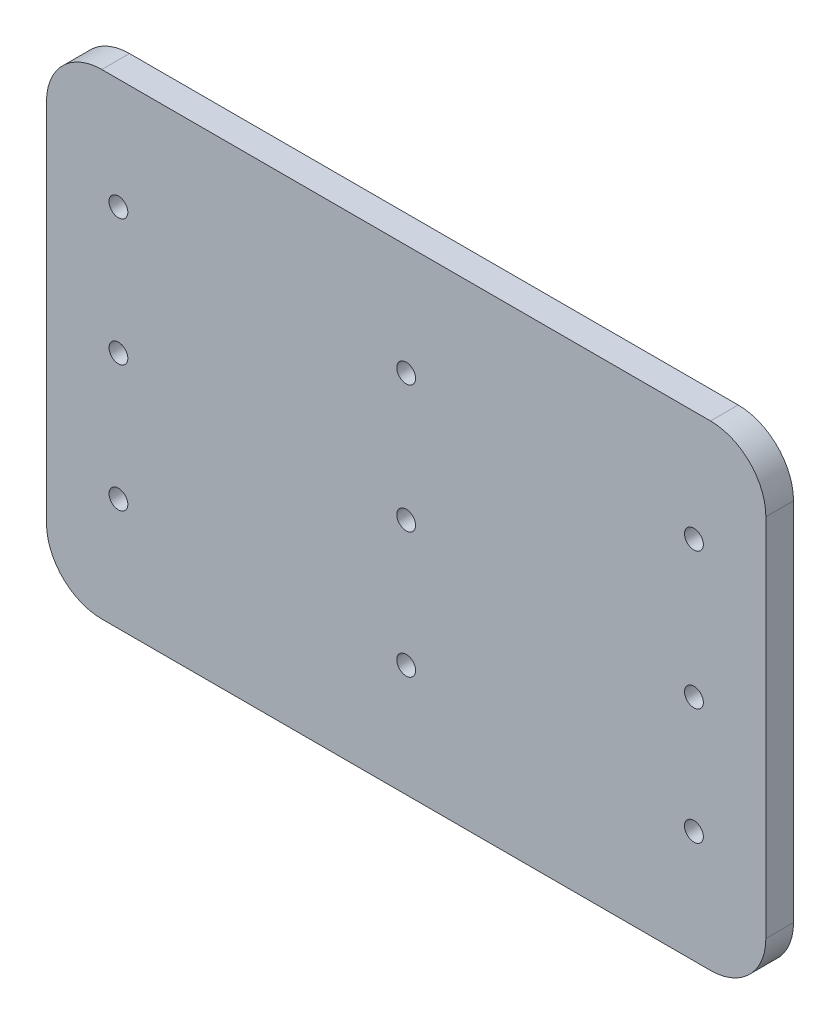
SolidWorks part; units mm, degrees
ref_plane "Front Plane" through (0, 0, 0) normal (0, 0, 1) x (1, 0, 0)
ref_plane "Top Plane" through (0, 0, 0) normal (0, 1, 0) x (1, 0, 0)
ref_plane "Right Plane" through (0, 0, 0) normal (1, 0, 0) x (0, 0, -1)
sketch "Sketch1" plane through (0, 0, 0) normal (0, 0, 1) x (1, 0, 0)
  line L0 (-52, 23) -> (52, 23) construction
  line L1 (-55, 43) -> (55, 43)
  line L2 (-65, 33) -> (-65, -33)
  line L3 (-55, -43) -> (55, -43)
  line L4 (65, 33) -> (65, -33)
  line L5 (-65, 43) -> (65, -43) construction
  line L6 (-65, -43) -> (65, 43) construction
  line L7 (-65, 43) -> (-52, 43)
  line L8 (-65, 43) -> (-65, 23)
  line L9 (-65, 23) -> (-52, 23)
  line L10 (-52, 43) -> (-52, 23)
  line L11 (-52, 23) -> (-52, -22.72) construction
  arc A0 (-65, 33) -> (-55, 43) centre (-55, 33) cw
  arc A1 (-55, -43) -> (-65, -33) centre (-55, -33) cw
  arc A2 (55, -43) -> (65, -33) centre (55, -33) ccw
  arc A3 (65, 33) -> (55, 43) centre (55, 33) ccw
  circle A4 centre (-52, 23) radius 1.7
  circle A5 centre (-52, -22.72) radius 1.7
  circle A6 centre (52, 23) radius 1.7
  circle A7 centre (52, -22.72) radius 1.7
  circle A8 centre (-52, 0.14) radius 1.7
  circle A9 centre (0, 0) radius 1.7
  circle A10 centre (0, -22.72) radius 1.7
  circle A11 centre (0, 23) radius 1.7
  circle A12 centre (52, -1.7) radius 1.7
  point P0 (0, 0)
  dimension "D3" = 10
  dimension "D4" = 10
  dimension "D5" = 10
  dimension "D6" = 10
  dimension "D1" = 130
  dimension "D2" = 86
extrude "Boss-Extrude1" add sketch "Sketch1" along normal blind 5 contours A4 L9 L2 A1 L3 A2 L4 A3 L1 L10 A7 A6 A5 | A4 L10 L1 A0 L2 L9
